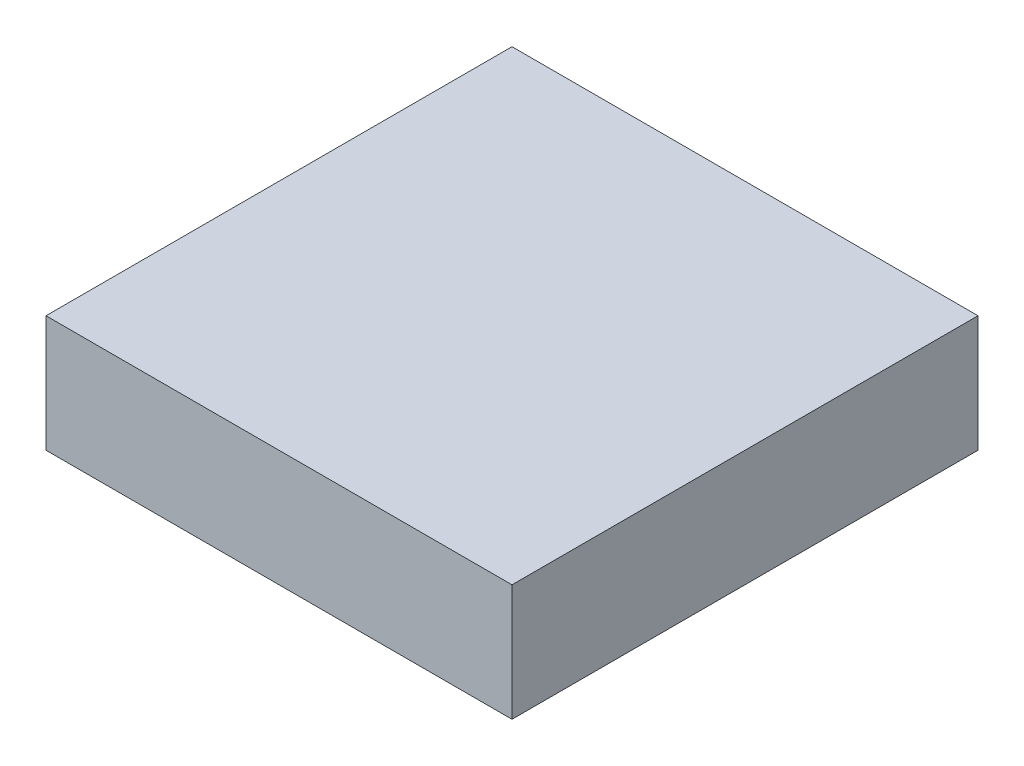
SolidWorks part; units mm, degrees
ref_plane "Front Plane" through (0, 0, 0) normal (0, 0, 1) x (1, 0, 0)
ref_plane "Top Plane" through (0, 0, 0) normal (0, 1, 0) x (1, 0, 0)
ref_plane "Right Plane" through (0, 0, 0) normal (1, 0, 0) x (0, 0, -1)
sketch "Sketch1" plane through (0, 0, 0) normal (0, 1, 0) x (1, 0, 0)
  line L1 (-10, -10) -> (10, -10)
  line L2 (-10, -10) -> (-10, 10)
  line L3 (-10, 10) -> (10, 10)
  line L4 (10, -10) -> (10, 10)
  dimension "D1" = 20
  dimension "D2" = 20
  dimension "D3" = 10
  dimension "D4" = 10
extrude "Boss-Extrude1" add sketch "Sketch1" along normal blind 5
